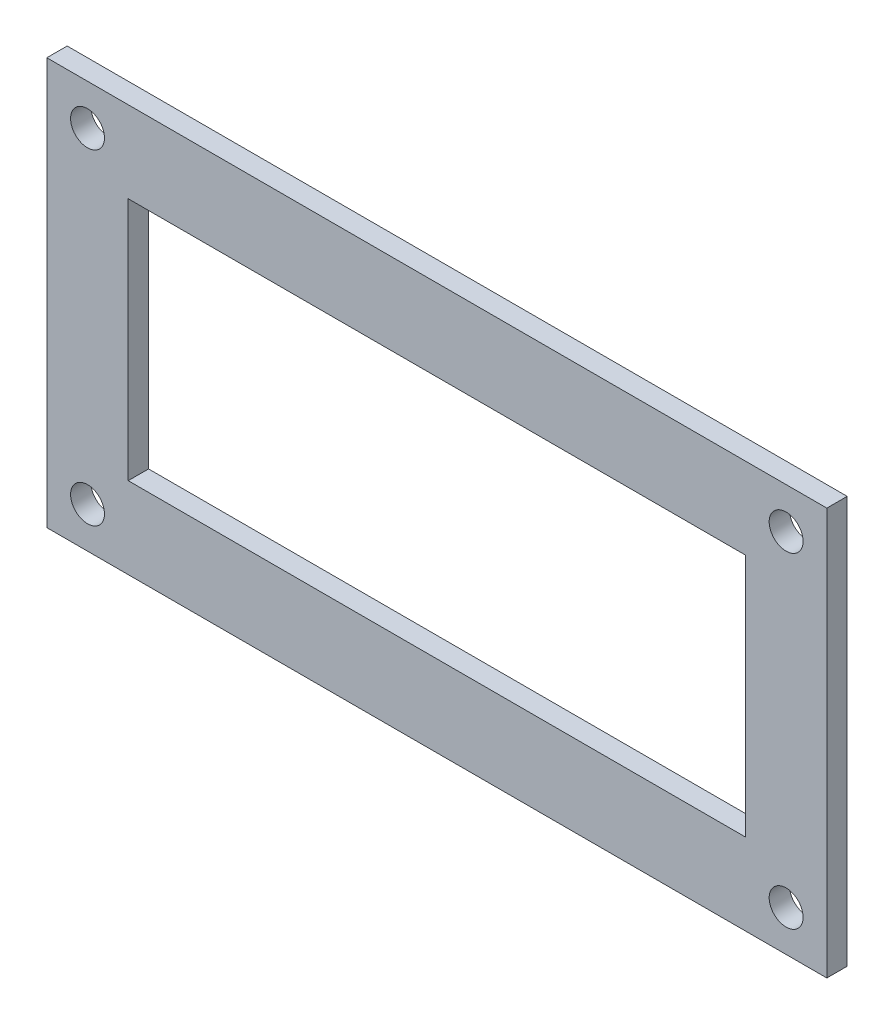
SolidWorks part; units mm, degrees
ref_plane "Front Plane" through (0, 0, 0) normal (0, 0, 1) x (1, 0, 0)
ref_plane "Top Plane" through (0, 0, 0) normal (0, 1, 0) x (1, 0, 0)
ref_plane "Right Plane" through (0, 0, 0) normal (1, 0, 0) x (0, 0, -1)
sketch "Sketch1" plane through (0, 0, 0) normal (0, 0, 1) x (1, 0, 0)
  line L1 (0, 0) -> (115, 0)
  line L2 (0, 0) -> (0, 60)
  line L3 (0, 60) -> (115, 60)
  line L4 (115, 0) -> (115, 60)
  line L5 (12, 48) -> (103, 48)
  line L6 (12, 48) -> (12, 12)
  line L7 (12, 12) -> (103, 12)
  line L8 (103, 48) -> (103, 12)
  circle A0 centre (6, 6) radius 2.5
  circle A1 centre (6, 54) radius 2.5
  circle A2 centre (109, 54) radius 2.5
  circle A3 centre (109, 6) radius 2.5
  dimension "D2" = 6
  dimension "D3" = 6
  dimension "D4" = 5
  dimension "D6" = 6
  dimension "D9" = 6
  dimension "D10" = 6
  dimension "D1" = 60
  dimension "D5" = 6
  dimension "D7" = 115
  dimension "D8" = 6
  dimension "D11" = 6
extrude "Boss-Extrude1" add sketch "Sketch1" along normal blind 3
